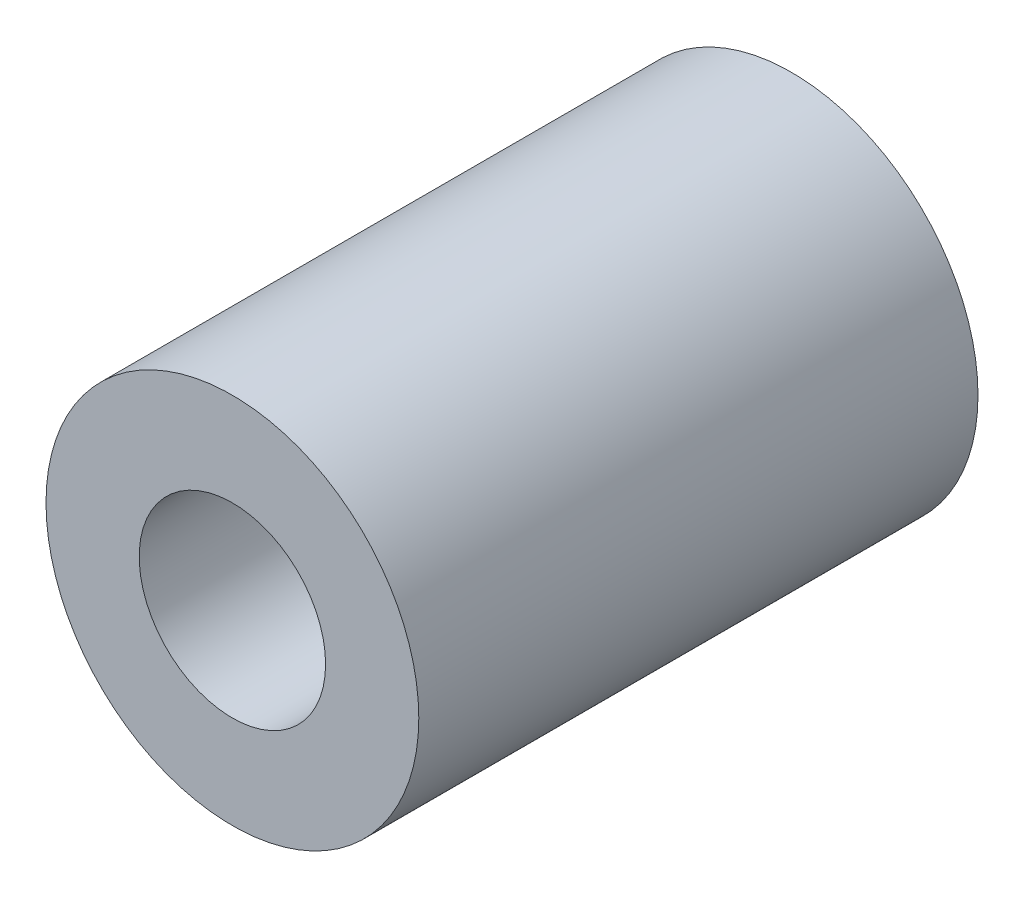
SolidWorks part; units mm, degrees
ref_plane "Alzado" through (0, 0, 0) normal (0, 0, 1) x (1, 0, 0)
ref_plane "Planta" through (0, 0, 0) normal (0, 1, 0) x (1, 0, 0)
ref_plane "Vista lateral" through (0, 0, 0) normal (1, 0, 0) x (0, 0, -1)
sketch "Croquis1" plane through (0, 0, 0) normal (0, 0, 1) x (1, 0, 0)
  circle A0 centre (0, 0) radius 1.5
  circle A1 centre (0, 0) radius 3
extrude "Saliente-Extruir1" add sketch "Croquis1" along normal blind 9 contours A0 | A1
